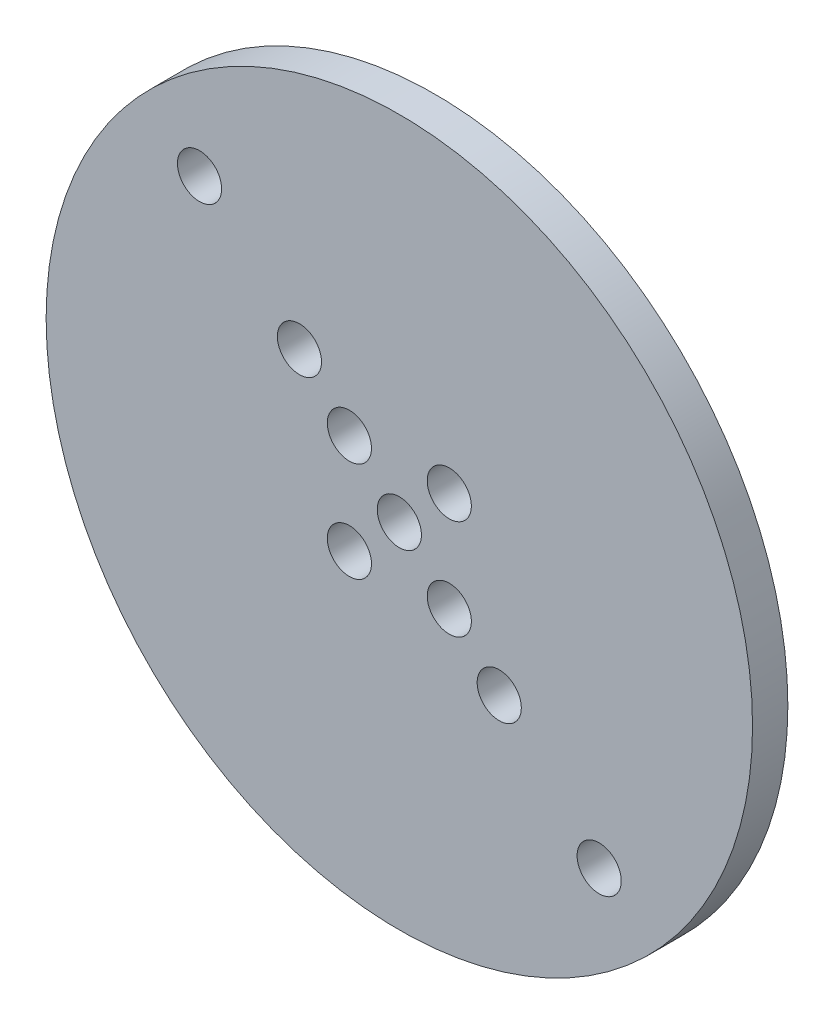
SolidWorks part; units mm, degrees
ref_plane "Front Plane" through (0, 0, 0) normal (0, 0, 1) x (1, 0, 0)
ref_plane "Top Plane" through (0, 0, 0) normal (0, 1, 0) x (1, 0, 0)
ref_plane "Right Plane" through (0, 0, 0) normal (1, 0, 0) x (0, 0, -1)
sketch "Sketch1" plane through (0, 0, 0) normal (0, 0, 1) x (1, 0, 0)
  circle A0 centre (0, 0) radius 63.5
  dimension "D1" = 127
extrude "Boss-Extrude1" add sketch "Sketch1" along normal blind 6.35
sketch "Sketch2" plane through (0, 0, 6.35) normal (0, 0, 1) x (1, 0, 0)
  line L0 (8.9803, 8.9803) -> (-8.9803, -8.9803) construction
  line L1 (-8.9803, 8.9803) -> (8.9803, 8.9803) construction
  line L2 (-8.9803, 8.9803) -> (-8.9803, -8.9803) construction
  line L3 (-8.9803, -8.9803) -> (8.9803, -8.9803) construction
  line L4 (8.9803, 8.9803) -> (8.9803, -8.9803) construction
  line L5 (-8.9803, 8.9803) -> (8.9803, -8.9803) construction
  line L6 (-35.921, 35.921) -> (35.921, -35.921) construction
  circle A0 centre (0, 0) radius 3.9688
  circle A1 centre (-8.9803, 8.9803) radius 3.9687
  circle A2 centre (8.9803, -8.9803) radius 3.9688
  circle A3 centre (8.9803, 8.9803) radius 3.9687
  circle A4 centre (-8.9803, -8.9803) radius 3.9688
  circle A5 centre (17.9605, -17.9605) radius 3.9688
  circle A6 centre (35.921, -35.921) radius 3.9687
  circle A7 centre (-17.9605, 17.9605) radius 3.9688
  circle A8 centre (-35.921, 35.921) radius 3.9687
  dimension "D1" = 7.9375
  dimension "D2" = 12.7
  dimension "D3" = 25.4
  dimension "D4" = 25.4
  dimension "D5" = 12.7
  dimension "D6" = 12.7
extrude "Cut-Extrude1" cut sketch "Sketch2" against normal through all
